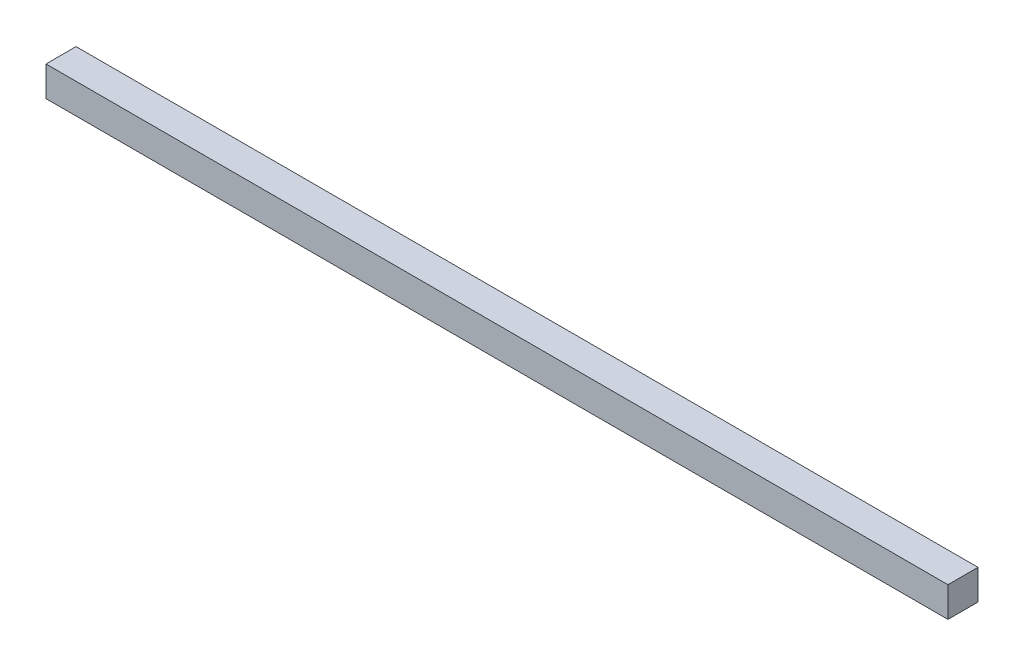
SolidWorks part; units mm, degrees
ref_plane "Front Plane" through (0, 0, 0) normal (0, 0, 1) x (1, 0, 0)
ref_plane "Top Plane" through (0, 0, 0) normal (0, 1, 0) x (1, 0, 0)
ref_plane "Right Plane" through (0, 0, 0) normal (1, 0, 0) x (0, 0, -1)
sketch "Sketch1" plane through (0, 0, 0) normal (0, 1, 0) x (1, 0, 0)
  line L1 (0, 0) -> (300, 0)
  line L2 (0, 0) -> (0, 10)
  line L3 (0, 10) -> (300, 10)
  line L4 (300, 0) -> (300, 10)
  dimension "D1" = 300
  dimension "w" = 10
extrude "Boss-Extrude1" add sketch "Sketch1" along normal blind 10
